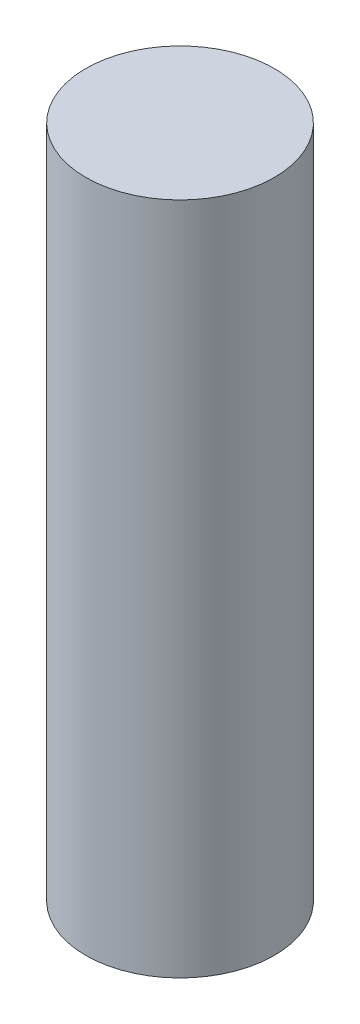
SolidWorks part; units mm, degrees
ref_plane "Plan de face" through (0, 0, 0) normal (0, 0, 1) x (1, 0, 0)
ref_plane "Plan de dessus" through (0, 0, 0) normal (0, 1, 0) x (1, 0, 0)
ref_plane "Plan de droite" through (0, 0, 0) normal (1, 0, 0) x (0, 0, -1)
sketch "Esquisse1" plane through (0, 0, 0) normal (0, 1, 0) x (1, 0, 0)
  circle A0 centre (0, 0) radius 10.5
  dimension "D1" = 21
extrude "Boss.-Extru.1" add sketch "Esquisse1" along normal mid plane 75
sketch "Esquisse2" plane through (0, 37.5, 0) normal (0, 1, 0) x (1, 0, 0)
  circle A0 centre (0, 0) radius 1
  dimension "D1" = 2
